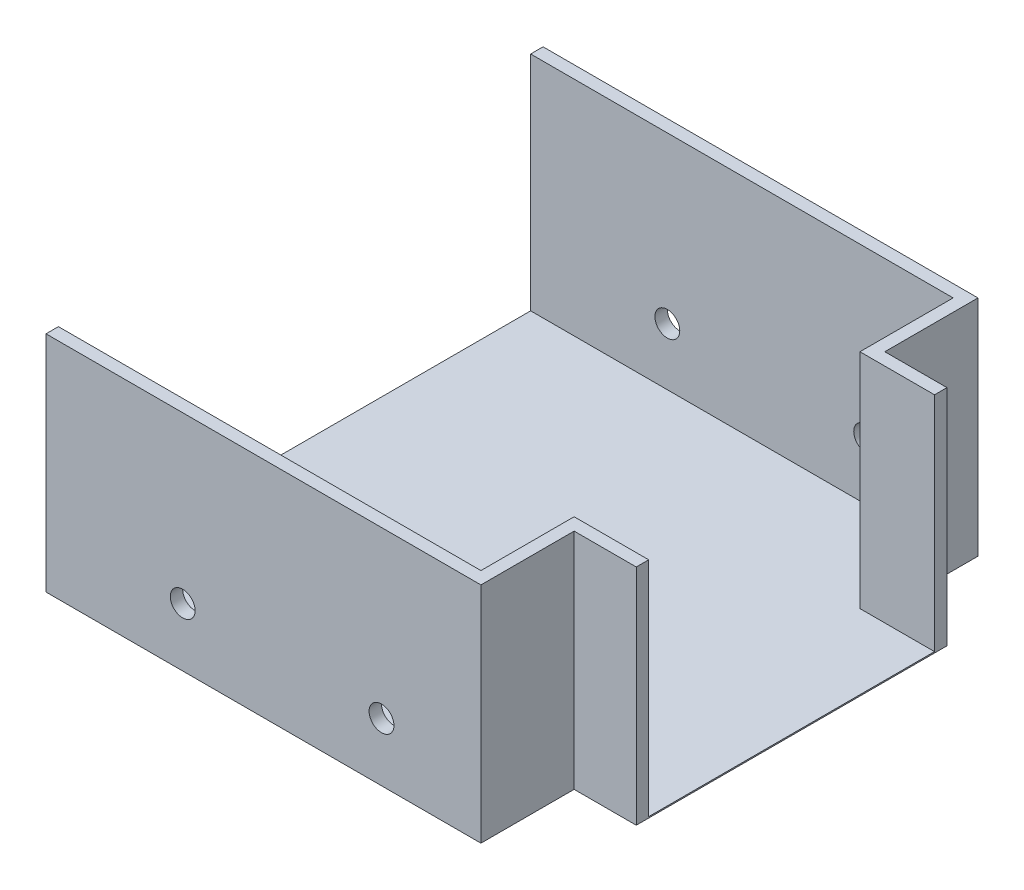
SolidWorks part; units mm, degrees
ref_plane "Front Plane" through (0, 0, 0) normal (0, 0, 1) x (1, 0, 0)
ref_plane "Top Plane" through (0, 0, 0) normal (0, 1, 0) x (1, 0, 0)
ref_plane "Right Plane" through (0, 0, 0) normal (1, 0, 0) x (0, 0, -1)
sketch "Sketch1" plane through (0, 0, 0) normal (0, 1, 0) x (1, 0, 0)
  line L1 (-175, 200) -> (175, 200)
  line L2 (-175, 200) -> (-175, -200)
  line L3 (-175, -200) -> (175, -200)
  line L4 (175, 200) -> (175, -200)
  line L5 (-175, 200) -> (175, -200) construction
  line L6 (-175, -200) -> (175, 200) construction
  line L7 (175, 125) -> (225, 125)
  line L8 (175, 125) -> (175, -125)
  line L9 (175, -125) -> (225, -125)
  line L10 (225, 125) -> (225, -125)
  point P0 (0, 0)
  dimension "D1" = 350
  dimension "D2" = 400
  dimension "D3" = 250
  dimension "D4" = 50
  dimension "D5" = 75
extrude "Boss-Extrude1" add sketch "Sketch1" along normal blind 180 contours L4 L1 L2 L3 | L10 L7 L4 L9
sketch "Sketch2" plane through (0, 180, 0) normal (0, 1, 0) x (1, 0, 0)
  line L0 (-175, 200) -> (-175, -200)
  line L1 (-175, -200) -> (175, -200)
  line L2 (175, -200) -> (175, -125)
  line L3 (175, -125) -> (225, -125)
  line L4 (225, -125) -> (225, 125)
  line L5 (225, 125) -> (175, 125)
  line L6 (175, 125) -> (175, 200)
  line L7 (175, 200) -> (-175, 200)
  line L8 (165, 190) -> (-165, 190)
  line L9 (-165, 190) -> (-165, -190)
  line L10 (-165, -190) -> (165, -190)
  line L11 (165, -190) -> (165, -115)
  line L12 (165, -115) -> (215, -115)
  line L13 (215, -115) -> (215, 115)
  line L14 (215, 115) -> (165, 115)
  line L15 (165, 115) -> (165, 190)
  dimension "D1" = 10
extrude "Cut-Extrude1" cut sketch "Sketch2" against normal blind 179 contours L14 L15 L8 L9 L10 L11 L12 L13
sketch "Sketch3" plane through (215, 0, 0) normal (-1, 0, 0) x (0, 0, 1)
  line L1 (-115, 1) -> (115, 1)
  line L2 (-115, 1) -> (-115, 180)
  line L3 (-115, 180) -> (115, 180)
  line L4 (115, 1) -> (115, 180)
extrude "Cut-Extrude2" cut sketch "Sketch3" against normal up to surface (10 mm away) up to face at (225, 90, 0)
sketch "Sketch4" plane through (-165, 0, 0) normal (1, 0, 0) x (0, 0, -1)
  line L0 (190, 1) -> (-190, 1) construction
  line L1 (-190, 1) -> (190, 1)
  line L2 (-190, 1) -> (-190, 180)
  line L3 (-190, 180) -> (190, 180)
  line L4 (190, 1) -> (190, 180)
  line L5 (190, 180) -> (-190, 180) construction
  line L6 (-190, 1) -> (-190, 180) construction
  dimension "D1" = 380
  dimension "D2" = 0
extrude "Cut-Extrude3" cut sketch "Sketch4" against normal up to surface (10 mm away) up to face at (-175, 90, 0)
sketch "Sketch5" plane through (0, 0, 200) normal (0, 0, 1) x (1, 0, 0)
  line L0 (175, 180) -> (175, 0) construction
  line L1 (-175, 0) -> (175, 0) construction
  circle A0 centre (95, 47) radius 10
  circle A1 centre (-65, 47) radius 10
  dimension "D1" = 20
  dimension "D2" = 80
  dimension "D3" = 160
  dimension "D4" = 47
extrude "Cut-Extrude4" cut sketch "Sketch5" against normal through all
